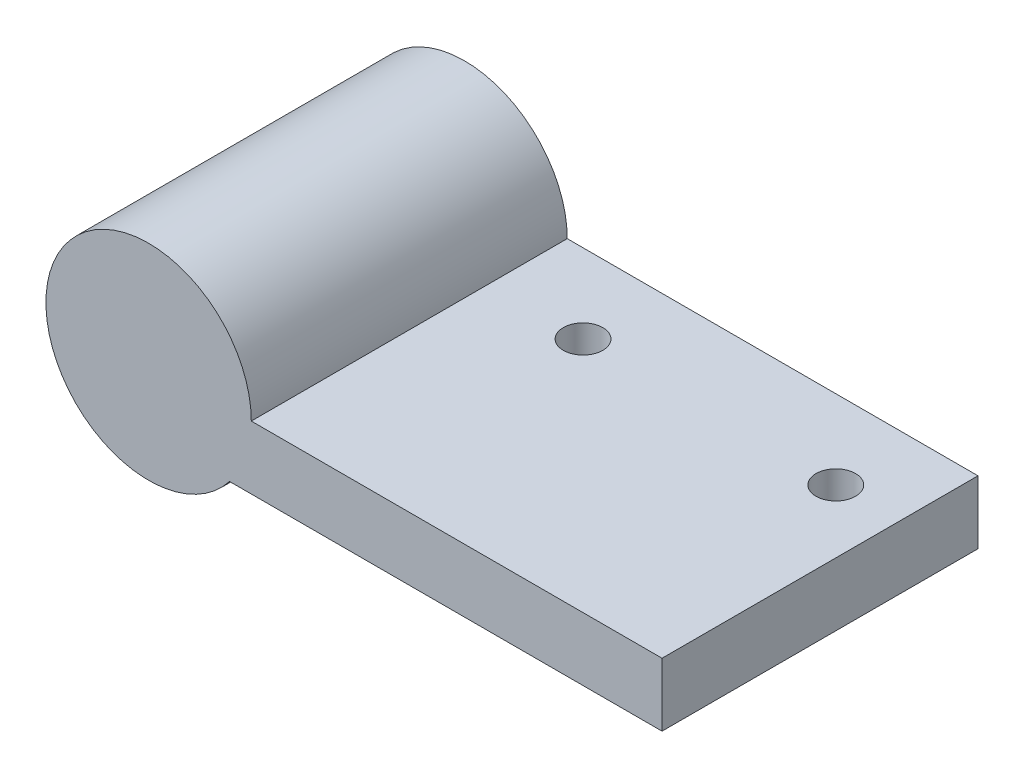
SolidWorks part; units mm, degrees
ref_plane "Спереди" through (0, 0, 0) normal (0, 0, 1) x (1, 0, 0)
ref_plane "Сверху" through (0, 0, 0) normal (0, 1, 0) x (1, 0, 0)
ref_plane "Справа" through (0, 0, 0) normal (1, 0, 0) x (0, 0, -1)
other "Configuration Table"
sketch "Эскиз1" plane through (0, 0, 0) normal (0, 0, 1) x (1, 0, 0)
  line L0 (5.1235, -4) -> (32.5, -4)
  line L1 (32.5, -4) -> (32.5, 0)
  line L2 (32.5, 0) -> (6.5, 0)
  circle A0 centre (0, 0) radius 4.15
  arc A1 (6.5, 0) -> (5.1235, -4) centre (0, 0) ccw
  circle A2 centre (39, 0) radius 6.5 construction
  dimension "D1" = 8.3
  dimension "D2" = 13
  dimension "D3" = 26
  dimension "D7" = 13
  dimension "D4" = 4
  dimension "D5" = 6.5
  dimension "D6" = 32.5
extrude "Бобышка-Вытянуть1" add sketch "Эскиз1" along normal blind 20
sketch "Эскиз2" plane through (0, 0, 20) normal (0, 0, 1) x (1, 0, 0)
  circle A0 centre (0, 0) radius 4.9232
extrude "Бобышка-Вытянуть2" add sketch "Эскиз2" against normal blind 3
sketch "Эскиз3" plane through (0, 0, 0) normal (0, 1, 0) x (1, 0, 0)
  line L8 (32.5, -20) -> (6.5, -20) construction
  line L9 (6.5, -20) -> (6.5, 0) construction
  circle A4 centre (12.5, -5) radius 1.25
  circle A5 centre (28.5, -5) radius 1.25
  dimension "D1" = 2.5
  dimension "D2" = 2.5
  dimension "D3" = 15
  dimension "D5" = 15
  dimension "D4" = 6
  dimension "D6" = 16
extrude "Вырез-Вытянуть1" cut sketch "Эскиз3" against normal blind 13
ref_plane "Плоскость1" through (17.5, 0, 0) normal (1, 0, 0) x (0, 0, -1)
